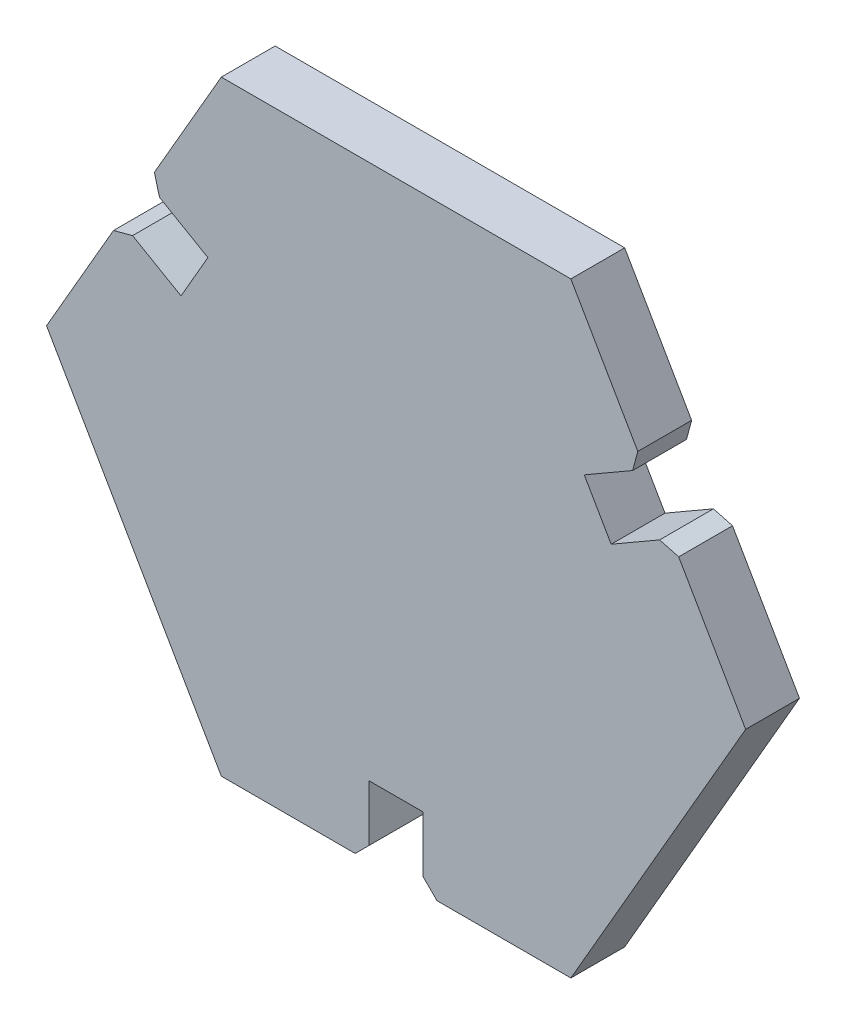
SolidWorks part; units mm, degrees
ref_plane "Front" through (0, 0, 0) normal (0, 0, 1) x (1, 0, 0)
ref_plane "Top" through (0, 0, 0) normal (0, 1, 0) x (1, 0, 0)
ref_plane "Right" through (0, 0, 0) normal (1, 0, 0) x (0, 0, -1)
sketch "Sketch1" plane through (0, 0, 0) normal (0, 0, 1) x (1, 0, 0)
  line L0 (0, 0) -> (25, 0) construction
  line L1 (25, 0) -> (12.5, 21.6506) construction
  line L2 (12.5, 21.6506) -> (-12.5, 21.6506) construction
  line L3 (-12.5, 21.6506) -> (-25, 0) construction
  line L4 (-25, 0) -> (-12.5, -21.6506) construction
  line L5 (-12.5, -21.6506) -> (12.5, -21.6506) construction
  line L6 (12.5, -21.6506) -> (25, 0) construction
  line L7 (0, 0) -> (18.75, 10.8253) construction
  line L8 (25, 0) -> (19.7125, 9.1582)
  line L9 (17.7875, 12.4924) -> (13.4574, 9.9924)
  line L10 (19.7125, 9.1582) -> (15.3824, 6.6582)
  line L11 (13.4574, 9.9924) -> (15.3824, 6.6582)
  line L12 (12.5, 21.6506) -> (17.7875, 12.4924)
  line L13 (12.5, -21.6506) -> (25, 0)
  line L14 (-12.5, 21.6506) -> (12.5, 21.6506)
  line L15 (-25, 0) -> (-12.5, -21.6506)
  line L18 (-1.925, -21.6506) -> (-1.925, -16.6506)
  line L19 (1.925, -16.6506) -> (-1.925, -16.6506)
  line L20 (1.925, -21.6506) -> (1.925, -16.6506)
  line L21 (12.5, -21.6506) -> (1.925, -21.6506)
  line L22 (-12.5, -21.6506) -> (-1.925, -21.6506)
  line L24 (-17.7875, 12.4924) -> (-13.4574, 9.9924)
  line L25 (-15.3824, 6.6582) -> (-13.4574, 9.9924)
  line L26 (-19.7125, 9.1582) -> (-15.3824, 6.6582)
  line L28 (-25, 0) -> (-19.7125, 9.1582)
  line L29 (-12.5, 21.6506) -> (-17.7875, 12.4924)
  circle A0 centre (0, 0) radius 21.6506 construction
  point P37 (0, 0)
  point P39 (0, 0)
  dimension "D1" = 3.85
  dimension "D2" = 5
  dimension "D3" = 25
  dimension "D5" = 330
  dimension "D4" = 3
extrude "Boss-Extrude1" add sketch "Sketch1" along normal blind 3.85
sketch "Sketch2" plane through (0, 0, 0) normal (0, 1, 0) x (1, 0, 0)
  line L0 (0, 0) -> (0, -19.2113) construction
chamfer "Chamfer1" distance 1 angle 45 6 edges at (1.925, -21.6506, 1.925) (-1.925, -21.6506, 1.925) (-19.7125, 9.1582, 1.925) (-17.7875, 12.4924, 1.925) (19.7125, 9.1582, 1.925) (17.7875, 12.4924, 1.925)
equation "\"entrance\"=5"
equation "\"D1@Boss-Extrude1\" = \"thick\""
equation "\"D2@Sketch1\"=\"entrance\""
equation "\"D1@Sketch1\"= \"thick\""
equation "\"thick\"=3.85"
